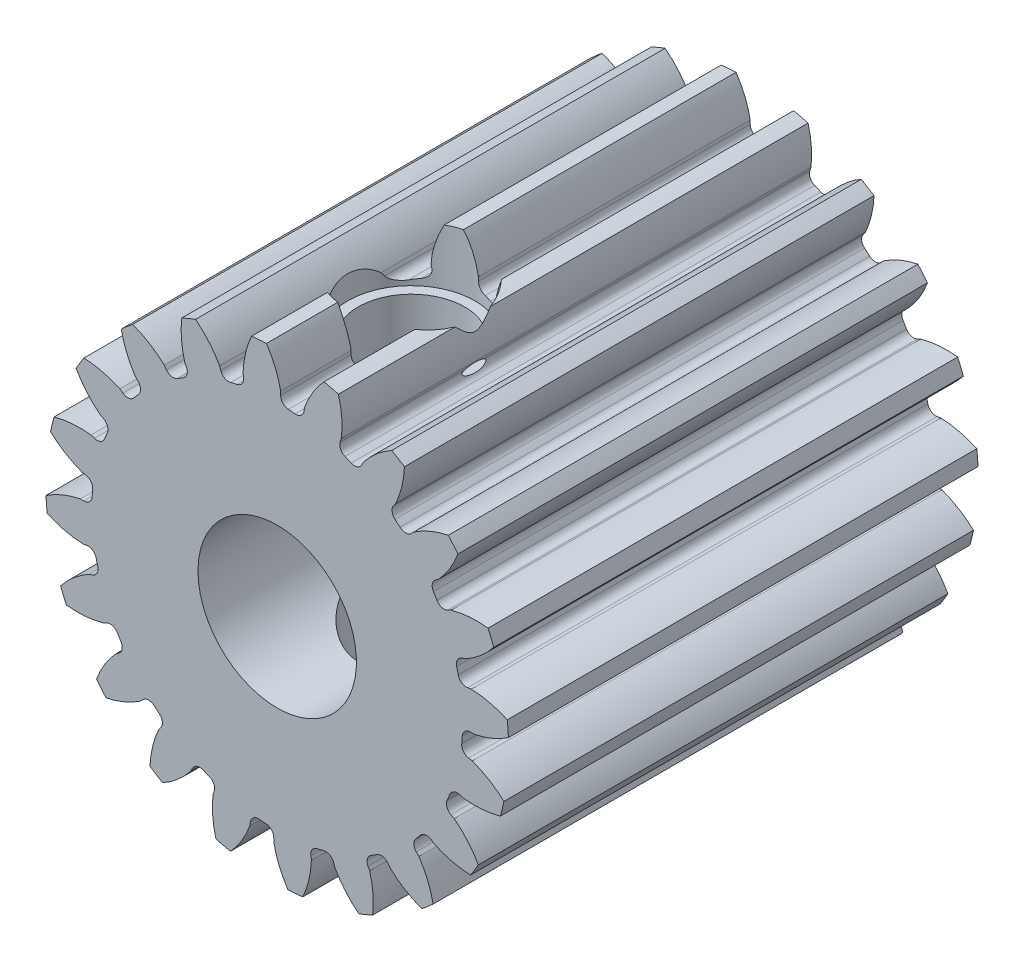
SolidWorks part; units mm, degrees
ref_plane "Front" through (0, 0, 0) normal (0, 0, 1) x (1, 0, 0)
ref_plane "Top" through (0, 0, 0) normal (0, 1, 0) x (1, 0, 0)
ref_plane "Right" through (0, 0, 0) normal (1, 0, 0) x (0, 0, -1)
sketch "Sketch1" plane through (0, 0, 0) normal (0, 0, 1) x (1, 0, 0)
  line L0 (-254, 0) -> (254, 0) construction
  circle A0 centre (0, 0) radius 8.763
  circle A1 centre (0, 0) radius 7.9375 construction
  circle A3 centre (0, 0) radius 7.0191 construction
  dimension "D1" = 0.9184
  dimension "D2" = 1.7439
  dimension "D3" = 0.8255
extrude "Boss-Extrude1" add sketch "Sketch1" against normal blind 304.8
sketch "Sketch3" plane through (0, 0, 0) normal (0, 0, 1) x (1, 0, 0)
  line L0 (0, 0) -> (0, 8.763) construction
  line L1 (-2.5511, 7.009) -> (0, 7.9375)
  line L2 (-9.5921, 7.9375) -> (9.5921, 7.9375) construction
  line L3 (-9.0136, 4.6568) -> (9.0136, 11.2182) construction
  line L4 (-2.5511, 7.009) -> (0, 0) construction
  line L5 (-5.3715, 5.175) -> (0, 0) construction
  line L6 (-5.3715, 5.175) -> (-1.1335, 9.5739) construction
  line L7 (-1.7721, 7.2452) -> (0, 0) construction
  line L8 (-1.7721, 7.2452) -> (0.0739, 7.6967) construction
  arc A0 (-2.5511, 7.009) -> (-5.3715, 5.175) centre (0, 0) ccw
  circle A1 centre (0, 0) radius 7.9375 construction
  circle A2 centre (0, 0) radius 7.4588 construction
  arc A3 (-2.5511, 7.009) -> (-1.7721, 7.2452) centre (0, 0) cw
  circle A4 centre (0, 0) radius 8.763 construction
  point P6 (0, 7.9375)
  dimension "D1" = 2.7148
  dimension "D3" = 6.1083
  dimension "D5" = 1.9003
  dimension "D2" = 3.3935
  dimension "D4" = 0.8144
sketch "Sketch4" plane through (0, 0, 0) normal (0, 0, 1) x (1, 0, 0)
  line L0 (0, 0) -> (0.6209, 7.8886) construction
  line L1 (0.1297, 7.4577) -> (0.1297, 7.0179)
  line L2 (0, 7.9375) -> (1.2417, 7.8398) construction
  line L3 (1.0386, 7.3861) -> (0.9698, 6.9518)
  line L4 (0.1297, 7.0179) -> (0, 0) construction
  line L5 (0, 0) -> (0, 8.763) construction
  line L6 (-5.3715, 5.175) -> (-1.1335, 9.5739) construction
  line L7 (-5.3715, 5.175) -> (-1.1335, 9.5739) construction
  arc A0 (0.9698, 6.9518) -> (0.1297, 7.0179) centre (0, 0) ccw
  arc A1 (0, 7.9375) -> (1.2417, 7.8398) centre (0, 0) cw construction
  circle A2 centre (0, 0) radius 7.9375 construction
  circle A3 centre (0, 0) radius 7.4588 construction
  circle A4 centre (0, 0) radius 7.0191 construction
  arc A5 (2.6173, 9.2787) -> (-1.1335, 9.5739) centre (0, 0) ccw
  spline S0 degree 2 poles (-1.1335, 9.5739) (-0.1134, 8.6803) (0.1297, 7.4577) knots 0 0 0 1 1 1
  spline S1 degree 2 poles (2.6173, 9.2787) (1.4699, 8.5557) (1.0386, 7.3861) knots 0 0 0 1 1 1
  dimension "D1" = 1.2468
extrude "Cut-Extrude1" cut sketch "Sketch4" against normal through all
fillet "Fillet1" radius 0.3117 2 edges at (0.9698, 6.9518, -152.4) (0.1297, 7.0179, -152.4)
pattern_circular "CirPattern1" count 20 over 360 about axis through (0, 0, -304.8) along (0, 0, 1) of "Cut-Extrude1", "Fillet1"
sketch "Pitch Dia" plane through (0, 0, 0) normal (0, 0, 1) x (1, 0, 0)
  circle A0 centre (0, 0) radius 7.9375 construction
  circle A1 centre (0, 0) radius 7.9375
sketch "Sketch5" plane through (0, 0, 0) normal (0, 1, 0) x (1, 0, 0)
  line L0 (0, 0) -> (0, -14.262) construction
  line L1 (0, 0) -> (3, 0)
  line L2 (0, 0) -> (0, 304.8)
  line L3 (0, 304.8) -> (16.5, 304.8)
  line L4 (16.5, 17.78) -> (16.5, 304.8)
  line L7 (16.5, 17.78) -> (3, 17.78)
  line L8 (3, 0) -> (3, 17.78)
  point P3 (0, 0)
  point P11 (0, 0)
  point P14 (0, 0)
  dimension "D1" = 6
  dimension "D2" = 17.78
  dimension "D3" = 33
revolve "Cut-Revolve1" cut sketch "Sketch5" angle 360 about L0
sketch "Sketch6" plane through (0, 0, 0) normal (0, 1, 0) x (1, 0, 0)
  line L0 (0, 17.78) -> (0, 0) construction
  circle A0 centre (0, 5.08) radius 2.413
  dimension "D1" = 4.826
  dimension "D2" = 5.08
extrude "Cut-Extrude2" cut sketch "Sketch6" along normal through all from offset 6.604
hole_wizard "#10-32 Tapped Hole1" positions "Sketch7" profile "Sketch8" tap size "#10-32" standard "ANSI Inch" end condition through all
sketch "Sketch7" plane through (0, 6.604, 0) normal (0, 1, 0) x (1, 0, 0)
  point P0 (0, 5.08)
sketch "Sketch8" plane through (0, 6.604, -5.08) normal (1, 0, 0) x (0, 0, 1)
  line L0 (0, 0) -> (0, 15.3576)
  line L1 (0, 15.3576) -> (2.0193, 15.3576)
  line L2 (2.0193, 15.3576) -> (2.0193, 0)
  line L5 (2.0193, 0) -> (0, 0)
  line L11 (0, -6.35) -> (0, 107.95) construction
  dimension "Thru Tap Drill Dia." = 4.0386
  dimension "Thru Tap Drill Depth" = 15.3576
cosmetic thread "Hole Thread1" parameters "D2"=4.826
equation "\"D2@Sketch3\" = \"D1@Sketch3\"*1.25"
equation "\"D3@Sketch3\" = \"D1@Sketch3\"+\"D2@Sketch3\""
equation "\"D4@Sketch3\" = \"D1@Sketch3\"*.3"
equation "\"D5@Sketch3\" = \"D1@Sketch3\"-\"D4@Sketch3\""
equation "\"D1@Sketch4\" = 1.5708/(\"Number of Teeth@Sketch1\"/\"Pitch Diameter@Sketch1\")"
equation "\"D1@CirPattern1\" = \"Number of Teeth@Sketch1\""
equation "\"D1@Fillet1\" = \"D1@Sketch4\"*.25"
equation "\"D1@Sketch1\" = 1.157/(\"Number of Teeth@Sketch1\"/\"Pitch Diameter@Sketch1\")"
